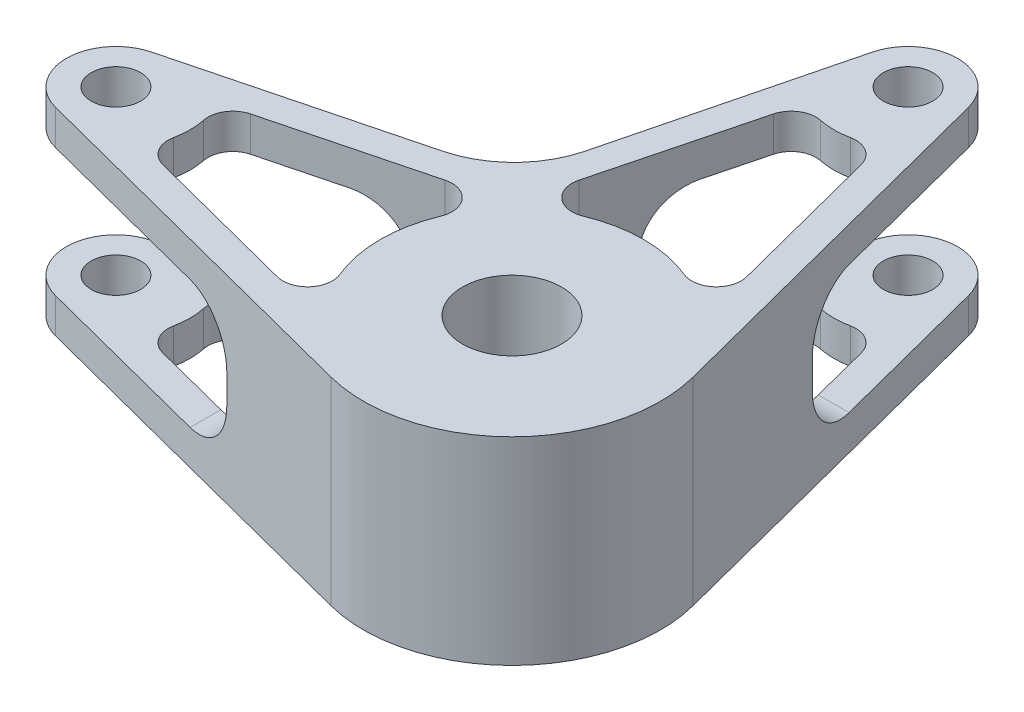
SolidWorks part; units mm, degrees
material "Alloy Steel"
ref_plane "Front Plane" through (0, 0, 0) normal (0, 0, 1) x (1, 0, 0)
ref_plane "Top Plane" through (0, 0, 0) normal (0, 1, 0) x (1, 0, 0)
ref_plane "Right Plane" through (0, 0, 0) normal (1, 0, 0) x (0, 0, -1)
sketch "Sketch1" plane through (0, 0, 0) normal (0, 1, 0) x (1, 0, 0)
  line L0 (0, 0) -> (0, 5) construction
  line L1 (0, 0) -> (-15, 0) construction
  line L2 (-41.25, -4.8412) -> (-3.75, -14.5237)
  line L3 (4.8412, 41.25) -> (14.5237, 3.75)
  line L4 (-10.7098, 17.9699) -> (-4.8483, 41.2222)
  line L5 (-41.25, 4.8412) -> (-34.0927, 6.6892)
  line L6 (-37.5, 0) -> (-34.3567, 0) construction
  line L7 (0, 37.5) -> (0, 40) construction
  line L9 (-41.25, 4.8412) -> (-17.8684, 10.8783)
  circle A0 centre (0, 0) radius 5
  circle A1 centre (0, 40) radius 2.5
  circle A2 centre (-40, 0) radius 2.5
  arc A3 (-3.75, -14.5237) -> (14.5237, 3.75) centre (0, 0) ccw
  arc A4 (4.8412, 41.25) -> (-4.8483, 41.2222) centre (0, 40) ccw
  arc A5 (-41.25, 4.8412) -> (-41.25, -4.8412) centre (-40, 0) ccw
  arc A6 (-17.8684, 10.8783) -> (-10.7098, 17.9699) centre (-20.3684, 20.5608) ccw
  arc A7 (-3.75, -14.5237) -> (14.5237, 3.75) centre (0, 0) ccw
  arc A8 (-4.0187, 42.9131) -> (-3.9287, 43.0928) centre (-3.5358, 42.7836) cw
  dimension "D1" = 10
  dimension "D2" = 5
  dimension "D4" = 5
  dimension "D6" = 10
  dimension "D8" = 2.5
  dimension "D9" = 10
  dimension "D10" = 0.5
  dimension "D3" = 40
  dimension "D5" = 40
extrude "Boss-Extrude1" add sketch "Sketch1" along normal blind 20
sketch3d "3DSketch2"
  line L0 (0, 20, -40) -> (0, 0, -40) construction
  line L1 (0, 20, -40) -> (0, 0, -40) construction
  line L2 (-40, 0, 0) -> (-40, 20, 0) construction
  line L3 (-40, 20, 0) -> (-40, 0, 0) construction
  line L4 (-40, 20, 0) -> (-40, 0, 0) construction
  line L5 (0, 20, 0) -> (0, 0, 0) construction
  line L6 (0, 20, 0) -> (0, 0, 0) construction
  point P10 (-40, 10, 0)
  point P11 (0, 10, -40)
  point P17 (0, 10, 0)
sketch3d "3DSketch3"
  line L0 (0, 10, 0) -> (0, 10, -40) construction
  line L1 (-40, 10, 0) -> (0, 10, 0) construction
sketch3d "3DSketch4"
  line L0 (0, 20, -40) -> (0, 0, -40) construction
  line L1 (0, 10, 0) -> (0, 10, -40) construction
  line L3 (0, 10, -40) -> (0, 10, -56.7349) construction
  line L4 (0, 16.4703, -40) -> (0, 16.4703, -25)
  line L5 (0, 3.5297, -40) -> (0, 3.5297, -25)
  line L6 (0, 8.5297, -20) -> (0, 11.4703, -20)
  line L7 (0, 16.4703, -40) -> (0, 16.4703, -54.3466)
  line L8 (0, 16.4703, -54.3466) -> (0, 3.5297, -54.3466)
  line L9 (0, 3.5297, -54.3466) -> (0, 3.5297, -40)
  arc A0 (0, 3.5297, -25) -> (0, 8.5297, -20) centre (0, 8.5297, -25) ccw
  arc A1 (0, 16.4703, -25) -> (0, 11.4703, -20) centre (0, 11.4703, -25) ccw
  point P15 (0, 3.5297, -20)
  point P16 (-5, 8.5297, -25)
  point P19 (0, 16.4703, -20)
  point P20 (5, 11.4703, -25)
  dimension "D3" = 5
  dimension "D1" = 6.4703
  dimension "D2" = 20
extrude "Cut-Extrude1" cut sketch "3DSketch4" along direction (1, 0, 0) on the side against the normal through all and the other way through all
sketch3d "3DSketch5"
  line L0 (-40, 10, 0) -> (0, 10, 0) construction
  line L1 (-40, 0, 0) -> (-40, 20, 0) construction
  line L2 (-40, 3.5297, 0) -> (-40, 16.4703, 0) construction
  line L3 (-40, 10, 0) -> (-48.3325, 10, 0) construction
  line L5 (-56.872, 16.4703, 0) -> (-22.9442, 16.4703, 0)
  line L6 (-56.872, 16.4703, 0) -> (-56.872, 3.5297, 0)
  line L7 (-56.872, 3.5297, 0) -> (-22.9442, 3.5297, 0)
  line L8 (-17.9442, 11.4703, 0) -> (-17.9442, 8.5297, 0)
  arc A0 (-22.9442, 3.5297, 0) -> (-17.9442, 8.5297, 0) centre (-22.9442, 8.5297, 0) ccw
  arc A1 (-22.9442, 16.4703, 0) -> (-17.9442, 11.4703, 0) centre (-22.9442, 11.4703, 0) ccw
  point P15 (-17.9442, 3.5297, 0)
  point P16 (-22.9442, 8.5297, 5)
  point P19 (-17.9442, 16.4703, 0)
  point P20 (-22.9442, 11.4703, -5)
  dimension "D2" = 5
  dimension "D1" = 6.4703
extrude "Cut-Extrude2" cut sketch "3DSketch5" along direction (0, 0, -1) on the side against the normal through all and the other way through all
sketch "Sketch2" plane through (0, 20, 0) normal (0, 1, 0) x (1, 0, 0)
  line L0 (0, 0) -> (-40, 0) construction
  line L1 (-41.25, 4.8412) -> (-17.8684, 10.8783) construction
  line L2 (-30.5897, 4.4953) -> (-17.1644, 7.9621)
  line L3 (-17.1644, 7.9621) -> (-15.2265, 8.4625)
  line L4 (-30.5897, 4.4953) -> (-30.8297, 4.4333)
  line L5 (-30.5897, -4.4953) -> (-30.8297, -4.4333)
  line L6 (-17.1644, -7.9621) -> (-15.2265, -8.4625)
  line L7 (-30.5897, -4.4953) -> (-17.1644, -7.9621)
  arc A0 (-12.2913, 5.0861) -> (-12.2913, -5.0861) centre (0, 0) ccw
  arc A2 (-32.6535, -1.5096) -> (-32.6535, 1.5096) centre (-40, 0) ccw
  circle A3 centre (-40, 0) radius 2.5 construction
  arc A4 (-15.2265, -8.4625) -> (-12.2913, -5.0861) centre (-14.6014, -6.0419) ccw
  arc A5 (-15.2265, 8.4625) -> (-12.2913, 5.0861) centre (-14.6014, 6.0419) cw
  arc A6 (-30.8297, -4.4333) -> (-32.6535, -1.5096) centre (-30.2047, -2.0127) cw
  arc A7 (-30.8297, 4.4333) -> (-32.6535, 1.5096) centre (-30.2047, 2.0127) ccw
  point P10 (-30.5897, 4.4953)
  point P13 (-17.1644, 7.9621)
  point P21 (-8.5564, -10.1849)
  point P24 (-8.5564, 10.1849)
  point P27 (-33.5011, -3.7435)
  point P30 (-33.5011, 3.7435)
  dimension "D1" = 2.5
  dimension "D2" = 5
  dimension "D3" = 3
  dimension "D4" = 3
extrude "Cut-Extrude3" cut sketch "Sketch2" against normal through all
pattern_circular "CirPattern1" count 2 over 90 about axis through (0, 0, 0) along (0, 1, 0) of "Cut-Extrude3"
